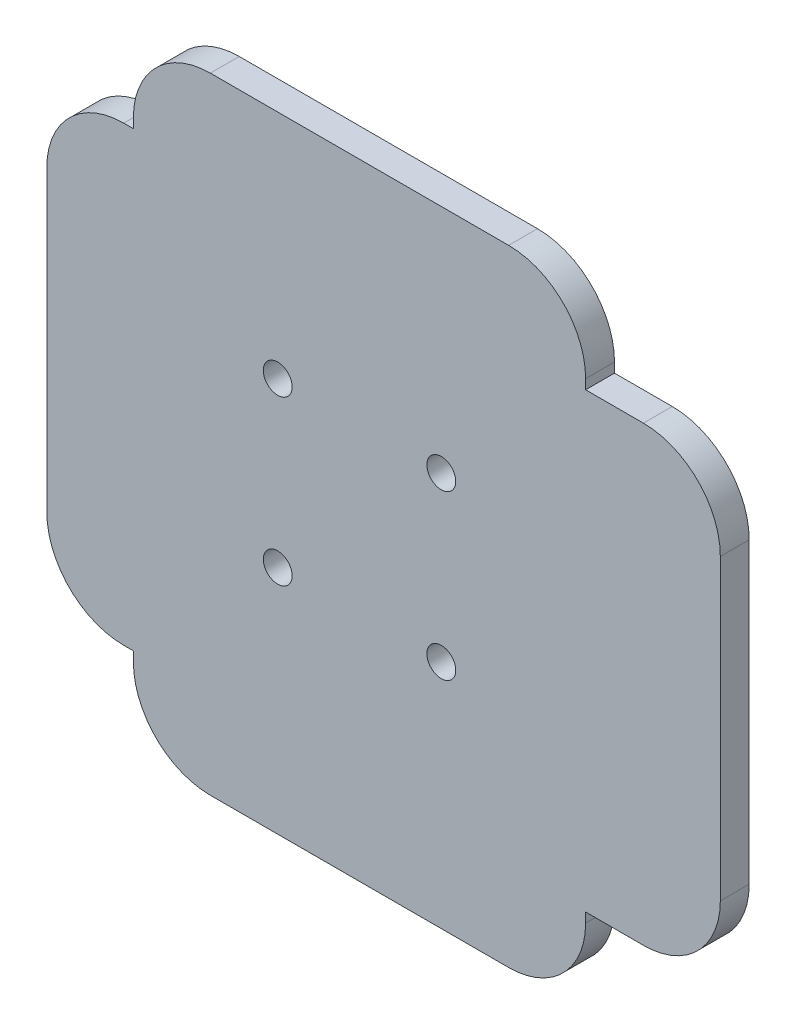
SolidWorks part; units mm, degrees
ref_plane "Plano frontal" through (0, 0, 0) normal (0, 0, 1) x (1, 0, 0)
ref_plane "Plano superior" through (0, 0, 0) normal (0, 1, 0) x (1, 0, 0)
ref_plane "Plano direito" through (0, 0, 0) normal (1, 0, 0) x (0, 0, -1)
sketch "Esboço1" plane through (0, 0, 0) normal (0, 0, 1) x (1, 0, 0)
  line L12 (7.5, -9.5) -> (38.5, -9.5)
  line L13 (46.5, -1.5) -> (46.5, -0.5)
  line L14 (46.5, -0.5) -> (52.5, -0.5)
  line L15 (60.5, 7.5) -> (60.5, 38.5)
  line L16 (52.5, 46.5) -> (46.5, 46.5)
  line L17 (46.5, 46.5) -> (46.5, 47.5)
  line L18 (38.5, 55.5) -> (7.5, 55.5)
  line L19 (-0.5, 47.5) -> (-0.5, 46.5)
  line L20 (-0.5, 46.5) -> (-1.5, 46.5)
  line L21 (-9.5, 38.5) -> (-9.5, 7.5)
  line L22 (-1.5, -0.5) -> (-0.5, -0.5)
  line L23 (-0.5, -0.5) -> (-0.5, -1.5)
  line L24 (7.5, -9.5) -> (38.5, -9.5)
  line L25 (46.5, -1.5) -> (46.5, -0.5)
  line L26 (46.5, -0.5) -> (52.5, -0.5)
  line L27 (60.5, 7.5) -> (60.5, 38.5)
  line L28 (52.5, 46.5) -> (46.5, 46.5)
  line L29 (46.5, 46.5) -> (46.5, 47.5)
  line L30 (38.5, 55.5) -> (7.5, 55.5)
  line L31 (-0.5, 47.5) -> (-0.5, 46.5)
  line L32 (-0.5, 46.5) -> (-1.5, 46.5)
  line L33 (-9.5, 38.5) -> (-9.5, 7.5)
  line L34 (-1.5, -0.5) -> (-0.5, -0.5)
  line L35 (-0.5, -0.5) -> (-0.5, -1.5)
  arc A8 (38.5, -9.5) -> (46.5, -1.5) centre (38.5, -1.5) ccw
  arc A9 (52.5, -0.5) -> (60.5, 7.5) centre (52.5, 7.5) ccw
  arc A10 (60.5, 38.5) -> (52.5, 46.5) centre (52.5, 38.5) ccw
  arc A11 (46.5, 47.5) -> (38.5, 55.5) centre (38.5, 47.5) ccw
  arc A12 (7.5, 55.5) -> (-0.5, 47.5) centre (7.5, 47.5) ccw
  arc A13 (-1.5, 46.5) -> (-9.5, 38.5) centre (-1.5, 38.5) ccw
  arc A14 (-9.5, 7.5) -> (-1.5, -0.5) centre (-1.5, 7.5) ccw
  arc A15 (-0.5, -1.5) -> (7.5, -9.5) centre (7.5, -1.5) ccw
  arc A16 (38.5, -9.5) -> (46.5, -1.5) centre (38.5, -1.5) ccw
  arc A17 (52.5, -0.5) -> (60.5, 7.5) centre (52.5, 7.5) ccw
  arc A18 (60.5, 38.5) -> (52.5, 46.5) centre (52.5, 38.5) ccw
  arc A19 (46.5, 47.5) -> (38.5, 55.5) centre (38.5, 47.5) ccw
  arc A20 (7.5, 55.5) -> (-0.5, 47.5) centre (7.5, 47.5) ccw
  arc A21 (-1.5, 46.5) -> (-9.5, 38.5) centre (-1.5, 38.5) ccw
  arc A22 (-9.5, 7.5) -> (-1.5, -0.5) centre (-1.5, 7.5) ccw
  arc A23 (-0.5, -1.5) -> (7.5, -9.5) centre (7.5, -1.5) ccw
  dimension "D1" = 0
extrude "Ressalto-extrusão1" add sketch "Esboço1" along normal blind 3
sketch "Esboço5" plane through (0, 0, 3) normal (0, 0, 1) x (1, 0, 0)
  line L4 (31.5, 34.5) -> (14.5, 34.5)
  line L5 (34.5, 14.5) -> (34.5, 31.5)
  line L6 (14.5, 11.5) -> (31.5, 11.5)
  line L7 (11.5, 31.5) -> (11.5, 14.5)
  line L8 (31.5, 34.5) -> (14.5, 34.5) construction
  line L9 (34.5, 14.5) -> (34.5, 31.5) construction
  line L10 (14.5, 11.5) -> (31.5, 11.5) construction
  line L11 (11.5, 31.5) -> (11.5, 14.5) construction
  circle A0 centre (31.5, 31.5) radius 1.5
  circle A1 centre (14.5, 31.5) radius 1.5
  circle A2 centre (14.5, 14.5) radius 1.5
  circle A3 centre (31.5, 14.5) radius 1.5
  arc A4 (34.5, 31.5) -> (31.5, 34.5) centre (31.5, 31.5) ccw
  arc A5 (31.5, 11.5) -> (34.5, 14.5) centre (31.5, 14.5) ccw
  arc A6 (11.5, 14.5) -> (14.5, 11.5) centre (14.5, 14.5) ccw
  arc A7 (14.5, 34.5) -> (11.5, 31.5) centre (14.5, 31.5) ccw
  arc A8 (34.5, 31.5) -> (31.5, 34.5) centre (31.5, 31.5) ccw construction
  arc A9 (31.5, 11.5) -> (34.5, 14.5) centre (31.5, 14.5) ccw construction
  arc A10 (11.5, 14.5) -> (14.5, 11.5) centre (14.5, 14.5) ccw construction
  arc A11 (14.5, 34.5) -> (11.5, 31.5) centre (14.5, 31.5) ccw construction
  dimension "D1" = 0
extrude "Corte-extrusão1" cut sketch "Esboço5" against normal through all
